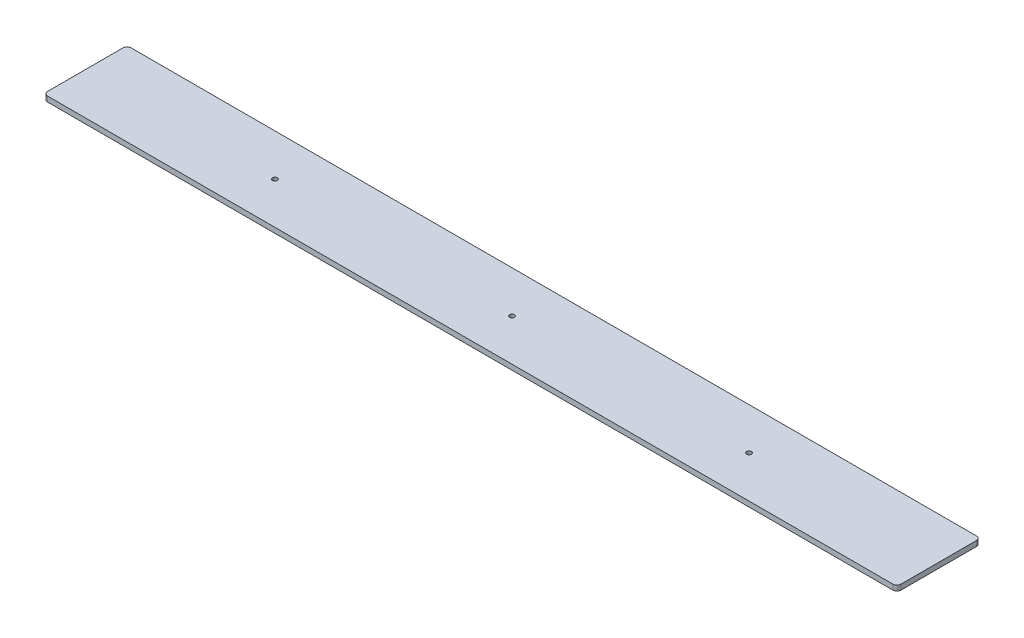
SolidWorks part; units mm, degrees
ref_plane "Front Plane" through (0, 0, 0) normal (0, 0, 1) x (1, 0, 0)
ref_plane "Top Plane" through (0, 0, 0) normal (0, 1, 0) x (1, 0, 0)
ref_plane "Right Plane" through (0, 0, 0) normal (1, 0, 0) x (0, 0, -1)
sketch "Sketch1" plane through (0, 0, 0) normal (0, 1, 0) x (1, 0, 0)
  line L1 (-259.5563, -25.4) -> (259.5562, -25.4)
  line L2 (-259.5563, -25.4) -> (-259.5563, 25.4)
  line L3 (-259.5563, 25.4) -> (259.5562, 25.4)
  line L4 (259.5562, -25.4) -> (259.5562, 25.4)
  line L5 (-259.5563, -25.4) -> (259.5562, 25.4) construction
  line L6 (-259.5563, 25.4) -> (259.5562, -25.4) construction
  point P0 (0, 0)
  dimension "D1" = 519.1125
  dimension "D2" = 50.8
extrude "Boss-Extrude1" add sketch "Sketch1" along normal blind 3.175
fillet "Fillet1" radius 2.54 4 edges at (-259.5563, 1.5875, -25.4) (-259.5563, 1.5875, 25.4) (259.5562, 1.5875, -25.4) (259.5562, 1.5875, 25.4)
hole_wizard "#4 Clearance Hole1" positions "Sketch2" profile "Sketch3" hole size "#4" standard "ANSI Inch" end condition through all
sketch "Sketch2" plane through (0, 0, 0) normal (0, -1, 0) x (-1, 0, 0)
  point P0 (-144.192, 0)
  point P3 (0, 0)
  point P6 (144.1996, 0)
sketch "Sketch3" plane through (144.192, 0, 0) normal (1, 0, 0) x (0, 0, -1)
  line L0 (0, 0) -> (0, 3.175)
  line L1 (0, 3.175) -> (1.4732, 3.175)
  line L2 (1.4732, 3.175) -> (1.4732, 0)
  line L5 (1.4732, 0) -> (0, 0)
  line L11 (0, -6.35) -> (0, 107.95) construction
  dimension "Thru Hole Dia." = 2.9464
  dimension "Thru Hole Depth" = 3.175
